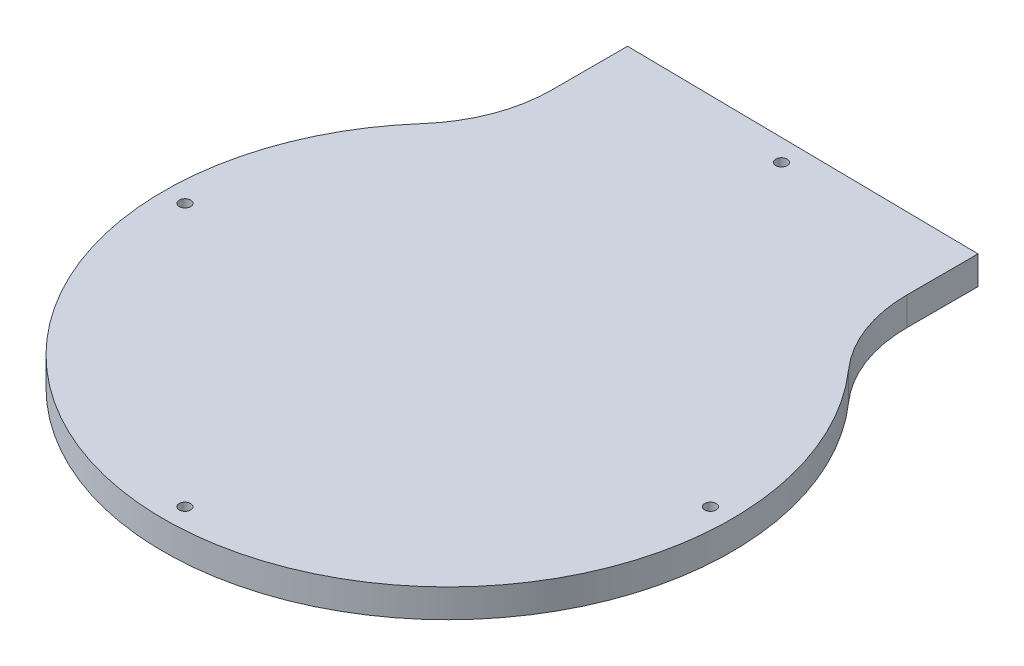
SolidWorks part; units mm, degrees
ref_plane "정면" through (0, 0, 0) normal (0, 0, 1) x (1, 0, 0)
ref_plane "윗면" through (0, 0, 0) normal (0, 1, 0) x (1, 0, 0)
ref_plane "우측면" through (0, 0, 0) normal (1, 0, 0) x (0, 0, -1)
ref_plane "평면1" through (0, 0, 0) normal (0, -1, 0) x (1, 0, 0)
sketch "스케치1" plane through (0, 0, 0) normal (0, -1, 0) x (1, 0, 0)
  line L0 (-24.9979, -39.6886) -> (-24.9979, -50.3275)
  line L1 (-24.9979, -50.3275) -> (24.9979, -49.6808)
  line L2 (24.9979, -49.6808) -> (24.9979, -39.6886)
  arc A0 (29.9986, -26.4591) -> (-29.9986, -26.4591) centre (0, 0) ccw
  arc A1 (-29.9986, -26.4591) -> (-24.9979, -39.6886) centre (-44.9979, -39.6886) cw
  arc A2 (24.9979, -39.6886) -> (29.9986, -26.4591) centre (44.9979, -39.6886) cw
  circle A3 centre (37, 0) radius 0.8
  circle A4 centre (0, 37) radius 0.8
  circle A5 centre (-37, 0) radius 0.8
  circle A6 centre (0, -47.0039) radius 0.8
extrude "보스-돌출1" add sketch "스케치1" against normal blind 4
